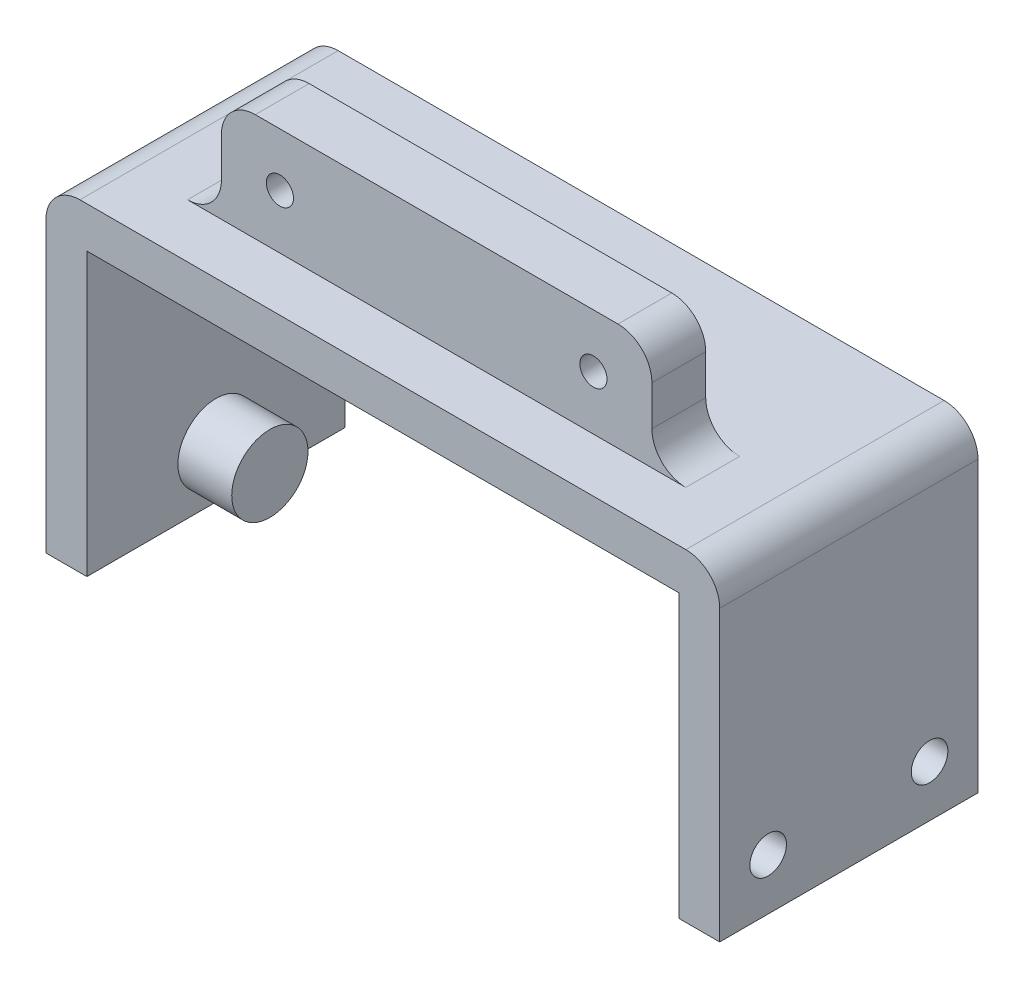
SolidWorks part; units mm, degrees
material "ABS"
ref_plane "Front" through (0, 0, 0) normal (0, 0, 1) x (1, 0, 0)
ref_plane "Top" through (0, 0, 0) normal (0, 1, 0) x (1, 0, 0)
ref_plane "Right" through (0, 0, 0) normal (1, 0, 0) x (0, 0, -1)
sketch "Sketch2" plane through (0, 0, 0) normal (1, 0, 0) x (0, 0, -1)
  line L0 (15.24, 38.1) -> (15.24, 0) construction
  line L1 (0, 0) -> (30.48, 0)
  line L2 (0, 0) -> (0, 38.1)
  line L3 (0, 38.1) -> (30.48, 38.1)
  line L4 (30.48, 0) -> (30.48, 38.1)
  circle A0 centre (5.715, 6.05) radius 2.159
  circle A1 centre (24.765, 6.05) radius 2.159
  point P9 (15.24, 6.05)
  dimension "D2" = 4.318
  dimension "D1" = 30.48
  dimension "D3" = 9.525
  dimension "D5" = 38.1
extrude "Boss-Extrude1" add sketch "Sketch2" along normal blind 4.826
sketch "Sketch3" plane through (0, 0, 0) normal (-1, 0, 0) x (0, 0, 1)
  line L1 (-30.48, 38.1) -> (0, 38.1)
  line L2 (-30.48, 38.1) -> (-30.48, 33.274)
  line L3 (-30.48, 33.274) -> (0, 33.274)
  line L4 (0, 38.1) -> (0, 33.274)
  dimension "D1" = 4.826
extrude "Boss-Extrude2" add sketch "Sketch3" along normal blind 74.676
sketch "Sketch4" plane through (0, 33.274, 0) normal (0, -1, 0) x (1, 0, 0)
  line L0 (-74.676, -30.48) -> (0, -30.48) construction
  line L1 (-74.676, 0) -> (-69.85, 0)
  line L2 (-74.676, 0) -> (-74.676, -30.48)
  line L3 (-74.676, -30.48) -> (-69.85, -30.48)
  line L4 (-69.85, 0) -> (-69.85, -30.48)
  dimension "D1" = 4.826
extrude "Boss-Extrude4" add sketch "Sketch4" along normal blind 33.274
sketch "Sketch5" plane through (0, 38.1, 0) normal (0, 1, 0) x (1, 0, 0)
  line L0 (-34.925, 30.48) -> (-34.925, 0) construction
  line L1 (4.826, 30.48) -> (-74.676, 30.48) construction
  line L2 (4.826, 0) -> (-74.676, 0) construction
  line L4 (-60.325, 6.35) -> (-9.525, 6.35)
  line L5 (-60.325, 6.35) -> (-60.325, 12.7)
  line L6 (-60.325, 12.7) -> (-9.525, 12.7)
  line L7 (-9.525, 6.35) -> (-9.525, 12.7)
  point P10 (-9.525, 9.525)
  dimension "D1" = 25.4
  dimension "D2" = 25.4
  dimension "D3" = 6.35
  dimension "D4" = 6.35
extrude "Boss-Extrude5" add sketch "Sketch5" along normal blind 12.7
sketch "Sketch6" plane through (0, 0, -12.7) normal (0, 0, -1) x (-1, 0, 0)
  line L5 (9.525, 50.8) -> (60.325, 50.8) construction
  line L6 (20.275, 50.9) -> (49.575, 50.9) construction
  line L7 (20.275, 50.9) -> (20.275, 38.1) construction
  line L8 (20.275, 38.1) -> (49.575, 38.1) construction
  line L9 (49.575, 50.9) -> (49.575, 38.1) construction
  circle A2 centre (16.425, 44.5) radius 1.6
  circle A3 centre (53.425, 44.5) radius 1.6
  point P4 (34.925, 50.9)
  point P7 (34.925, 50.8)
extrude "Cut-Extrude1" cut sketch "Sketch6" against normal up to next
fillet "Fillet2" radius 4 6 edges at (-74.676, 38.1, -15.24) (4.826, 38.1, -15.24) (-60.325, 50.8, -9.525) (-60.325, 38.1, -9.525) (-9.525, 38.1, -9.525) (-9.525, 50.8, -9.525)
sketch "Sketch7" plane through (-69.85, 0, 0) normal (1, 0, 0) x (0, 0, -1)
  line L0 (30.48, 0) -> (0, 0) construction
  line L1 (15.24, 33.274) -> (15.24, 0) construction
  line L2 (30.48, 33.274) -> (0, 33.274) construction
  circle A0 centre (15.24, 6.096) radius 4.5
  dimension "D1" = 6.096
  dimension "D2" = 9
extrude "Boss-Extrude6" add sketch "Sketch7" along normal blind 6.35
